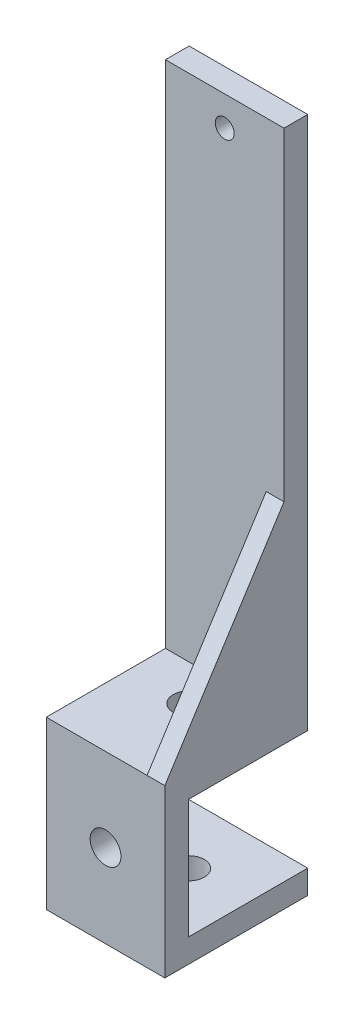
SolidWorks part; units mm, degrees
ref_plane "前视基准面" through (0, 0, 0) normal (0, 0, 1) x (1, 0, 0)
ref_plane "上视基准面" through (0, 0, 0) normal (0, 1, 0) x (1, 0, 0)
ref_plane "右视基准面" through (0, 0, 0) normal (1, 0, 0) x (0, 0, -1)
sketch "草图1" plane through (0, 0, 0) normal (0, 0, 1) x (1, 0, 0)
  line L1 (-9.2097, 42.7391) -> (-29.2097, 42.7391)
  line L2 (-9.2097, 42.7391) -> (-9.2097, -47.2609)
  line L3 (-9.2097, -47.2609) -> (-29.2097, -47.2609)
  line L4 (-29.2097, 42.7391) -> (-29.2097, -47.2609)
  dimension "D1" = 90
  dimension "D2" = 20
extrude "凸台-拉伸1" add sketch "草图1" along normal blind 4
sketch "草图2" plane through (0, 0, 4) normal (0, 0, 1) x (1, 0, 0)
  line L0 (-29.2097, -43.2609) -> (-9.2097, -43.2609)
  line L1 (-29.2097, 42.7391) -> (-29.2097, -47.2609) construction
  line L2 (-9.2097, -47.2609) -> (-9.2097, 42.7391) construction
  line L3 (-29.2097, -47.2609) -> (-9.2097, -47.2609) construction
  line L4 (-29.2097, -43.2609) -> (-29.2097, -47.2609)
  line L5 (-29.2097, -47.2609) -> (-9.2097, -47.2609)
  line L6 (-9.2097, -47.2609) -> (-9.2097, -43.2609)
  dimension "D1" = 4
extrude "凸台-拉伸2" add sketch "草图2" along normal blind 20.1
sketch "草图3" plane through (0, -47.2609, 0) normal (0, -1, 0) x (-1, 0, 0)
  line L0 (9.2097, -20.1) -> (29.2097, -20.1)
  line L1 (9.2097, -24.1) -> (9.2097, 0) construction
  line L2 (29.2097, -24.1) -> (29.2097, 0) construction
  line L3 (29.2097, -24.1) -> (9.2097, -24.1) construction
  line L4 (9.2097, -20.1) -> (9.2097, -24.1)
  line L5 (9.2097, -24.1) -> (29.2097, -24.1)
  line L6 (29.2097, -24.1) -> (29.2097, -20.1)
  dimension "D1" = 4
extrude "凸台-拉伸3" add sketch "草图3" along normal blind 24.1
sketch "草图4" plane through (0, 0, 20.1) normal (0, 0, -1) x (-1, 0, 0)
  line L0 (9.2097, -67.3609) -> (29.2097, -67.3609)
  line L1 (9.2097, -71.3609) -> (9.2097, -47.2609) construction
  line L2 (29.2097, -71.3609) -> (29.2097, -47.2609) construction
  line L3 (29.2097, -71.3609) -> (9.2097, -71.3609) construction
  line L4 (9.2097, -67.3609) -> (9.2097, -71.3609)
  line L5 (9.2097, -71.3609) -> (29.2097, -71.3609)
  line L6 (29.2097, -71.3609) -> (29.2097, -67.3609)
  dimension "D1" = 4
extrude "凸台-拉伸4" add sketch "草图4" along normal blind 20.1
sketch "草图5" plane through (0, -47.2609, 0) normal (0, -1, 0) x (-1, 0, 0)
  circle A0 centre (19.2097, -10.0948) radius 2.6
  dimension "D1" = 5.2
extrude "切除-拉伸1" cut sketch "草图5" against normal blind 20
sketch "草图6" plane through (0, 0, 20.1) normal (0, 0, -1) x (-1, 0, 0)
  circle A0 centre (19.2097, -57.3109) radius 2.6
  dimension "D1" = 5.2
extrude "切除-拉伸2" cut sketch "草图6" against normal blind 20
sketch "草图7" plane through (0, -67.3609, 0) normal (0, 1, 0) x (1, 0, 0)
  circle A0 centre (-19.2097, -10.05) radius 2.6
  dimension "D1" = 5.2
extrude "切除-拉伸3" cut sketch "草图7" against normal blind 20
sketch "草图9" plane through (0, 0, 0) normal (0, 0, -1) x (-1, 0, 0)
  circle A0 centre (19.2097, 37.7391) radius 1.6
  circle A1 centre (19.2097, -38.2609) radius 1.6
  dimension "D3" = 3.2
  dimension "D4" = 3.2
extrude "切除-拉伸4" cut sketch "草图9" against normal blind 20
sketch "草图10" plane through (-9.2097, 0, 0) normal (1, 0, 0) x (0, 0, -1)
  line L0 (-4, -11.8483) -> (-24.1, -43.2609)
  line L1 (-4, -43.2609) -> (-4, 42.7391) construction
  line L2 (-4, -11.8483) -> (-4, -43.2609)
  line L3 (-4, -43.2609) -> (-24.1, -43.2609)
extrude "凸台-拉伸5" add sketch "草图10" against normal blind 3
